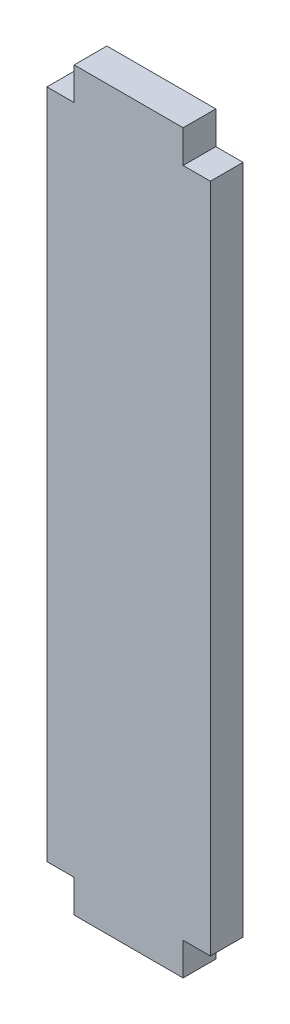
SolidWorks part; units mm, degrees
material "Acrylic (Medium-high impact)"
ref_plane "Ebene vorne" through (0, 0, 0) normal (0, 0, 1) x (1, 0, 0)
ref_plane "Ebene oben" through (0, 0, 0) normal (0, 1, 0) x (1, 0, 0)
ref_plane "Ebene rechts" through (0, 0, 0) normal (1, 0, 0) x (0, 0, -1)
sketch "Sketch1" plane through (0, 0, 0) normal (0, 0, 1) x (1, 0, 0)
  line L0 (0, 33.8) -> (0, -33.8) construction
  line L1 (5, -33.8) -> (-5, -33.8)
  line L2 (5, -33.8) -> (5, 33.8)
  line L3 (5, 33.8) -> (-5, 33.8)
  line L4 (-5, -33.8) -> (-5, 33.8)
  line L5 (5, -33.8) -> (-5, 33.8) construction
  line L6 (5, 33.8) -> (-5, -33.8) construction
  line L7 (-5, 30.8) -> (-7.5, 30.8)
  line L8 (-5, 30.8) -> (-5, -30.8)
  line L9 (-5, -30.8) -> (-7.5, -30.8)
  line L10 (-7.5, 30.8) -> (-7.5, -30.8)
  line L11 (5, 30.8) -> (7.5, 30.8)
  line L12 (5, 30.8) -> (5, -30.8)
  line L13 (5, -30.8) -> (7.5, -30.8)
  line L14 (7.5, 30.8) -> (7.5, -30.8)
  point P0 (0, 0)
  dimension "D1" = 10
  dimension "D2" = 67.6
  dimension "D3" = 3
  dimension "D4" = 3
  dimension "D5" = 15
extrude "Boss-Extrude1" add sketch "Sketch1" along normal blind 3 contours L7 L10 L9 L4 | L4 L1 L2 L3 | L14 L11 L2 L13
